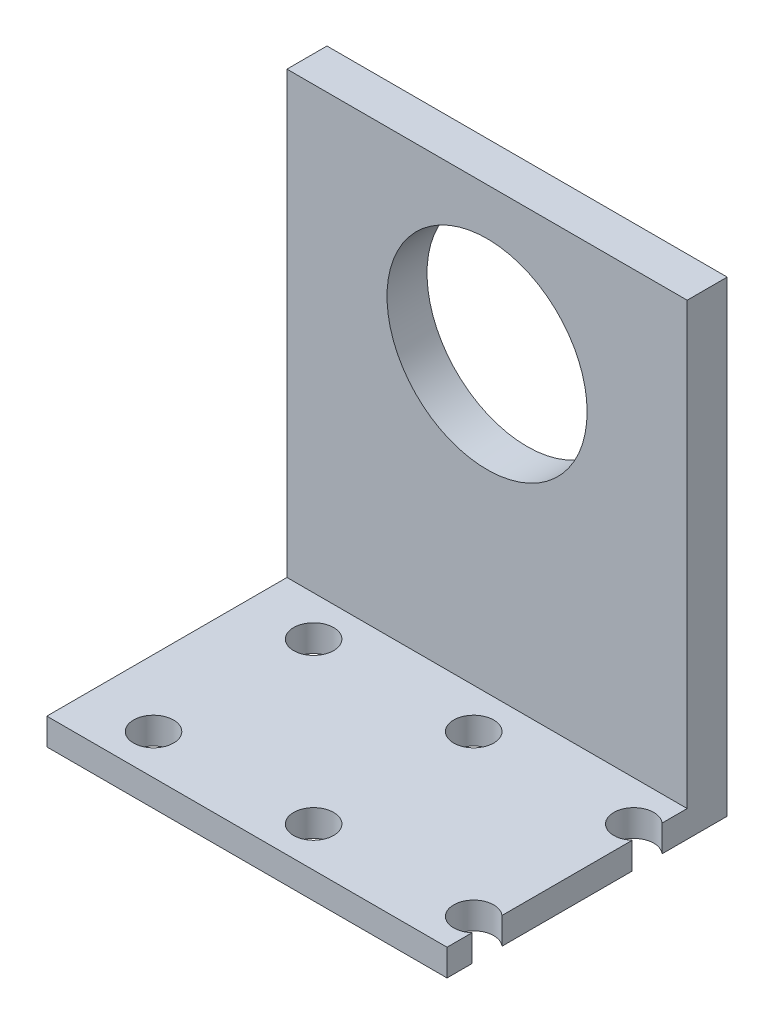
SolidWorks part; units mm, degrees
ref_plane "Front Plane" through (0, 0, 0) normal (0, 0, 1) x (1, 0, 0)
ref_plane "Top Plane" through (0, 0, 0) normal (0, 1, 0) x (1, 0, 0)
ref_plane "Right Plane" through (0, 0, 0) normal (1, 0, 0) x (0, 0, -1)
sketch "Sketch1" plane through (0, 0, 0) normal (1, 0, 0) x (0, 0, -1)
  line L0 (0, 0) -> (18, 0)
  line L1 (18, 0) -> (18, 33)
  line L2 (18, 33) -> (21, 33)
  line L3 (21, 33) -> (21, -2)
  line L4 (21, -2) -> (0, -2)
  line L5 (0, -2) -> (0, 0)
  dimension "D1" = 3
  dimension "D2" = 2
  dimension "D3" = 35
  dimension "D4" = 21
extrude "Boss-Extrude1" add sketch "Sketch1" along normal blind 30
sketch "Sketch2" plane through (0, 0, -18) normal (0, 0, 1) x (1, 0, 0)
  line L0 (0, 22) -> (30, 22) construction
  line L1 (0, 33) -> (0, 0) construction
  line L2 (30, 33) -> (30, 0) construction
  line L3 (30, -2) -> (0, -2) construction
  circle A0 centre (15, 22) radius 7.5
  dimension "D2" = 15
  dimension "D1" = 24
extrude "Cut-Extrude1" cut sketch "Sketch2" against normal blind 30 contours A0
sketch "Sketch5" plane through (0, 0, 0) normal (0, 1, 0) x (1, 0, 0)
  line L0 (0, 18) -> (0, 0) construction
  line L1 (30, 0) -> (0, 0) construction
  circle A0 centre (5, 3) radius 1.5
  circle A1 centre (17, 3) radius 1.5
  circle A2 centre (29, 3) radius 1.5
  circle A3 centre (17, 15) radius 1.5
  circle A4 centre (29, 15) radius 1.5
  circle A5 centre (5, 15) radius 1.5
  dimension "D1" = 3
  dimension "D2" = 5
  dimension "D3" = 3
  dimension "D6" = 12
  dimension "D8" = 12
  dimension "D7" = 30
  dimension "D9" = 18
  dimension "D4" = 3
  dimension "D5" = 2
extrude "Cut-Extrude2" cut sketch "Sketch5" against normal blind 30
